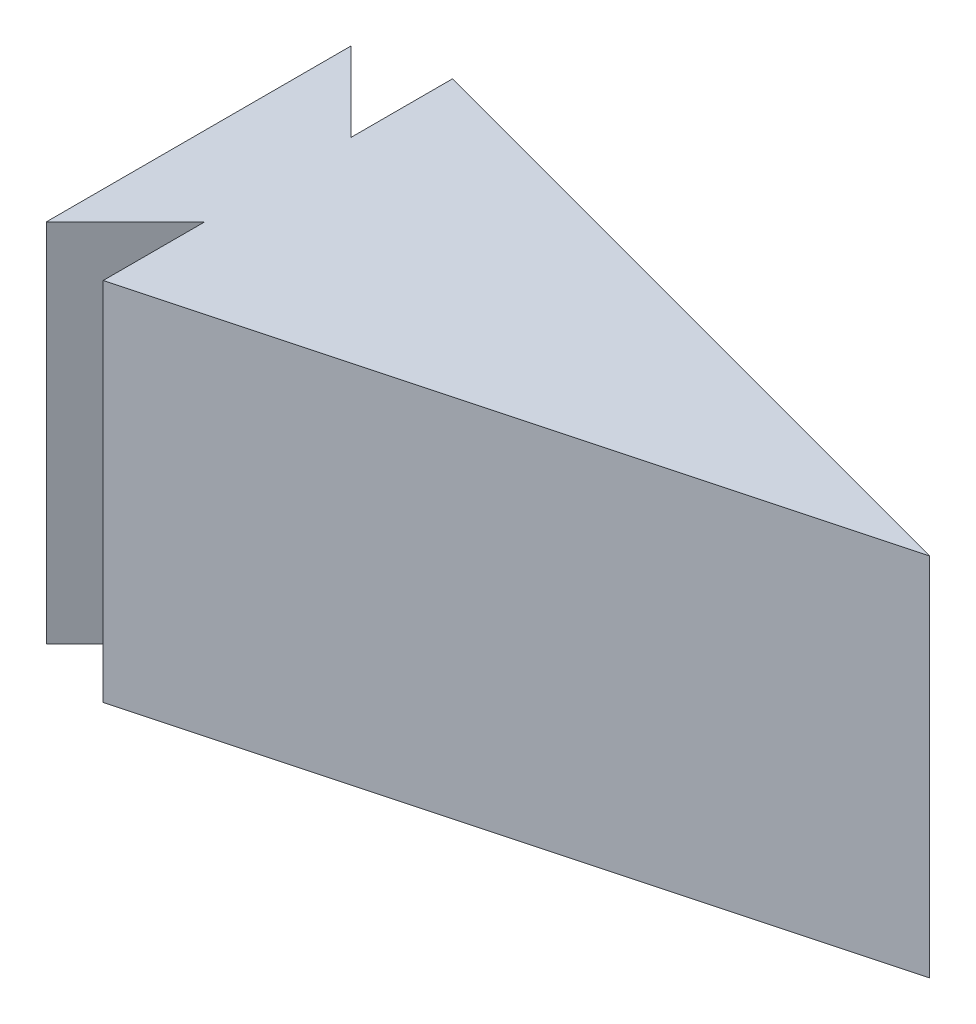
SolidWorks part; units mm, degrees
ref_plane "Front Plane" through (0, 0, 0) normal (0, 0, 1) x (1, 0, 0)
ref_plane "Top Plane" through (0, 0, 0) normal (0, 1, 0) x (1, 0, 0)
ref_plane "Right Plane" through (0, 0, 0) normal (1, 0, 0) x (0, 0, -1)
sketch "Sketch1" plane through (0, 0, 0) normal (0, 1, 0) x (1, 0, 0)
  line L0 (0, 0) -> (0, 31.75)
  line L1 (0, 31.75) -> (8.255, 23.495)
  line L2 (8.255, 23.495) -> (8.255, 34.0808)
  line L3 (8.255, 34.0808) -> (76.2, 15.875)
  line L4 (76.2, 15.875) -> (8.255, -2.3308)
  line L5 (8.255, -2.3308) -> (8.255, 8.255)
  line L6 (8.255, 8.255) -> (0, 0)
  dimension "D1" = 31.75
  dimension "D2" = 15.24
  dimension "D3" = 45
  dimension "D4" = 45
  dimension "D5" = 75
  dimension "D6" = 75
  dimension "D7" = 76.2
extrude "Boss-Extrude1" add sketch "Sketch1" along normal blind 38.1
